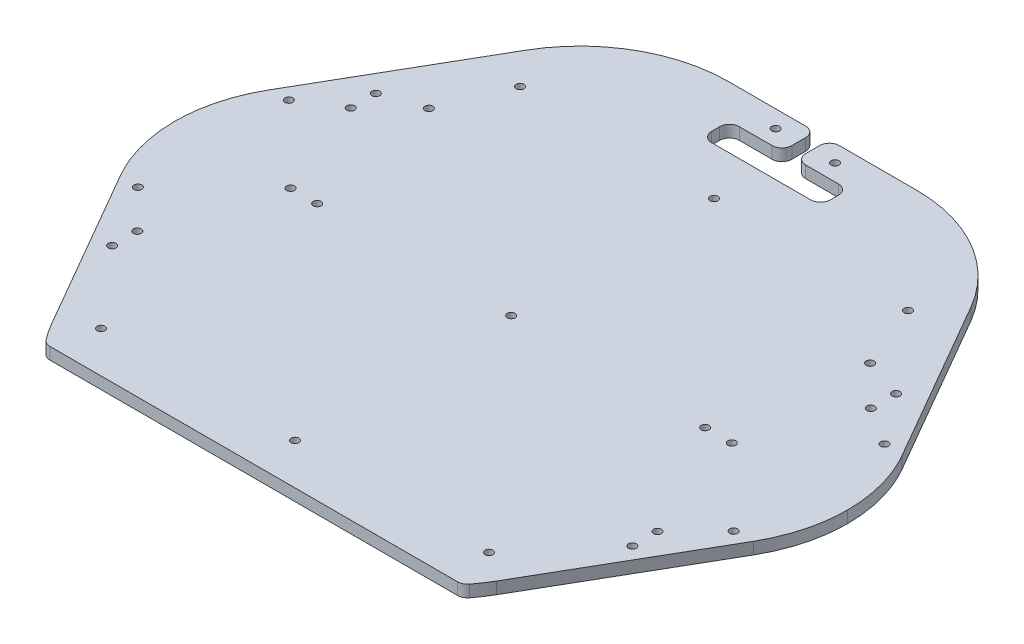
SolidWorks part; units mm, degrees
ref_plane "Front Plane" through (0, 0, 0) normal (0, 0, 1) x (1, 0, 0)
ref_plane "Top Plane" through (0, 0, 0) normal (0, 1, 0) x (1, 0, 0)
ref_plane "Right Plane" through (0, 0, 0) normal (1, 0, 0) x (0, 0, -1)
ref_plane "Plane1" through (0, 6, 0) normal (0, 1, 0) x (1, 0, 0)
sketch "Sketch1" plane through (0, 6, 0) normal (0, 1, 0) x (1, 0, 0)
  line L0 (112.4519, -119.7724) -> (159.9519, -37.5)
  line L1 (159.9519, 37.5) -> (90.8013, 157.2724)
  line L2 (90.8013, 157.2724) -> (-90.8013, 157.2724)
  line L3 (-90.8013, 157.2724) -> (-159.9519, 37.5)
  line L4 (-159.9519, -37.5) -> (-112.4519, -119.7724)
  line L5 (-105.3856, -130) -> (105.3856, -130)
  spline S0 degree 3 poles (105.3856, -130) (105.779, -129.4973) (106.1723, -128.9946) (106.5657, -128.4919) (108.7286, -125.7279) (110.697, -122.8118) (112.4519, -119.7724) knots 2.452075 2.452075 2.452075 2.452075 2.477608 2.477608 2.477608 2.617994 2.617994 2.617994 2.617994
  spline S1 degree 3 poles (159.9519, -37.5) (162.0898, -33.7968) (165.8426, -25.7861) (169.2445, -13.0899) (169.9999, -4.2761) (170, 0) knots 2.617994 2.617994 2.617994 2.617994 2.789036 2.97055 3.141593 3.141593 3.141593 3.141593
  spline S2 degree 3 poles (170, 0) (169.9999, 4.276) (169.2445, 13.0899) (165.8426, 25.7861) (162.0898, 33.7968) (159.9519, 37.5) knots 3.141593 3.141593 3.141593 3.141593 3.312635 3.494149 3.665191 3.665191 3.665191 3.665191
  spline S3 degree 3 poles (-159.9519, 37.5) (-162.0898, 33.7968) (-165.8426, 25.7861) (-169.2445, 13.0899) (-169.9999, 4.2761) (-170, 0) knots 5.759587 5.759587 5.759587 5.759587 5.930629 6.112143 6.283185 6.283185 6.283185 6.283185
  spline S4 degree 3 poles (-170, 0) (-169.9999, -4.2761) (-169.2445, -13.0899) (-165.8426, -25.7861) (-162.0898, -33.7968) (-159.9519, -37.5) knots 6.283185 6.283185 6.283185 6.283185 6.454228 6.635742 6.806784 6.806784 6.806784 6.806784
  spline S5 degree 3 poles (-112.4519, -119.7724) (-110.697, -122.8118) (-108.7286, -125.7279) (-106.5657, -128.4919) (-106.1723, -128.9946) (-105.779, -129.4973) (-105.3856, -130) knots 0.523599 0.523599 0.523599 0.523599 0.663985 0.663985 0.663985 0.689517 0.689517 0.689517 0.689517
extrude "Boss-Extrude1" add sketch "Sketch1" against normal blind 6
sketch "Sketch2" plane through (0, 0, 0) normal (0, -1, 0) x (1, 0, 0)
  line L0 (3.5, -157.2724) -> (3.5, -140.2724)
  line L1 (3.5, -140.2724) -> (30, -140.2724)
  line L2 (30, -140.2724) -> (30, -126.2724)
  line L3 (30, -126.2724) -> (-30, -126.2724)
  line L4 (-30, -126.2724) -> (-30, -140.2724)
  line L5 (-30, -140.2724) -> (-3.5, -140.2724)
  line L6 (-3.5, -140.2724) -> (-3.5, -157.2724)
  line L7 (-3.5, -157.2724) -> (3.5, -157.2724)
extrude "Cut-Extrude1" cut sketch "Sketch2" against normal through all
hole_wizard "M3.5 Clearance Hole1" positions "Sketch4" profile "Sketch3" hole size "M3.5" standard "ANSI Metric"
sketch "Sketch4" plane through (0, 0, 0) normal (0, -1, 0) x (-1, 0, 0)
  point P0 (98, -109.22)
  point P1 (-98, 102.4382)
  point P2 (98, 102.4382)
  point P3 (0, 102.4382)
  point P4 (0, -109.22)
  point P5 (0, 0)
  point P6 (-97.9932, 0)
  point P7 (97.9932, 0)
  point P8 (111.4552, 69.85)
  point P9 (111.4552, 0)
  point P10 (-111.4552, 69.85)
  point P11 (-111.4552, 0)
  point P12 (-98, -109.22)
  point P13 (131.4, 50.3)
  point P14 (-131.4, 50.3)
  point P15 (131.4, -70.2)
  point P16 (-131.4, -70.2)
  point P17 (131.4, 63)
  point P18 (-131.4, 63)
  point P19 (131.4, -57.5)
  point P20 (-131.4, -57.5)
  point P21 (15, 148.6)
  point P22 (-15, 148.6)
  point P23 (150.47, 38.1)
  point P24 (150.47, -38.1)
  point P25 (-150.47, 38.1)
  point P26 (-150.47, -38.1)
sketch "Sketch3" plane through (-98, 0, 109.22) normal (1, 0, 0) x (0, 0, -1)
  line L0 (0, 0) -> (0, 6.0001)
  line L1 (0, 6.0001) -> (1.9748, 6.0001)
  line L2 (1.9748, 6.0001) -> (1.9748, 0)
  line L5 (1.9748, 0) -> (0, 0)
  line L11 (0, -6.35) -> (0, 107.95) construction
  dimension "Thru Hole Dia." = 3.9496
  dimension "Thru Hole Depth" = 6.0001
fillet "Fillet1" radius 5.0207 10 edges at (-105.3856, 3, 130) (3.5, 3, -140.2724) (-30, 3, -126.2724) (-30, 3, -140.2724) (-3.5, 3, -140.2724) (30, 3, -140.2724) (105.3856, 3, 130) (30, 3, -126.2724)
fillet "Fillet2" radius 74.9585 2 edges at (90.8013, 3, -157.2724) (-90.8013, 3, -157.2724)
